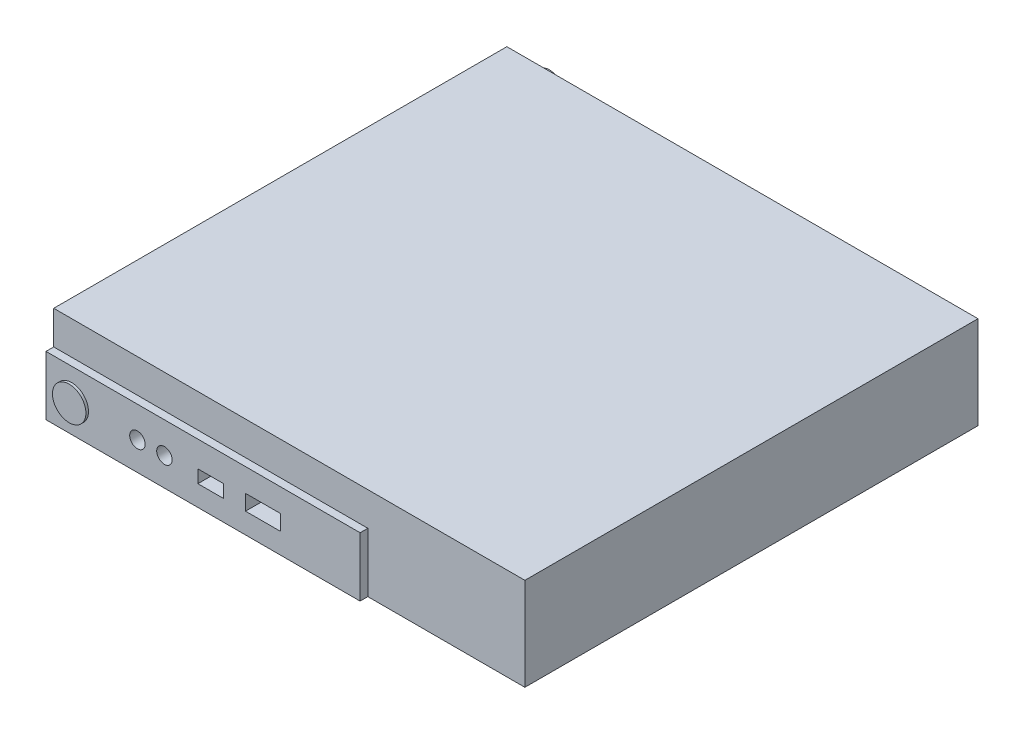
SolidWorks part; units mm, degrees
ref_plane "Front" through (0, 0, 0) normal (0, 0, 1) x (1, 0, 0)
ref_plane "Top" through (0, 0, 0) normal (0, 1, 0) x (1, 0, 0)
ref_plane "Right" through (0, 0, 0) normal (1, 0, 0) x (0, 0, -1)
sketch "草图1" plane through (0, 0, 0) normal (0, 1, 0) x (1, 0, 0)
  line L1 (-91.5, -89.5) -> (91.5, -89.5)
  line L2 (-91.5, -89.5) -> (-91.5, 89.5)
  line L3 (-91.5, 89.5) -> (91.5, 89.5)
  line L4 (91.5, -89.5) -> (91.5, 89.5)
  line L5 (-91.5, -89.5) -> (91.5, 89.5) construction
  line L6 (-91.5, 89.5) -> (91.5, -89.5) construction
  point P0 (0, 0)
  dimension "D1" = 179
  dimension "D2" = 183
extrude "凸台-拉伸1" add sketch "草图1" along normal blind 36
sketch "草图2" plane through (0, 0, 89.5) normal (0, 0, 1) x (1, 0, 0)
  line L0 (-91.5, 36) -> (-91.5, 23)
  line L1 (-91.5, 23) -> (30.5, 23)
  line L2 (30.5, 23) -> (30.5, 0)
  line L3 (-91.5, 0) -> (91.5, 0) construction
  line L4 (30.5, 0) -> (91.5, 0)
  line L5 (91.5, 0) -> (91.5, 36)
  line L6 (91.5, 36) -> (-91.5, 36)
  dimension "D1" = 122
  dimension "D2" = 23
extrude "切除-拉伸1" cut sketch "草图2" against normal blind 3
sketch "草图3" plane through (0, 0, 89.5) normal (0, 0, 1) x (1, 0, 0)
  line L0 (-91.5, 0) -> (30.5, 0) construction
  line L1 (-32.5, 13) -> (-22.5, 13)
  line L2 (-32.5, 13) -> (-32.5, 8)
  line L3 (-32.5, 8) -> (-22.5, 8)
  line L4 (-14, 14) -> (-0.5, 14)
  line L5 (-14, 14) -> (-14, 8)
  line L6 (-14, 8) -> (-0.5, 8)
  line L7 (-0.5, 14) -> (-0.5, 8)
  line L8 (-22.5, 13) -> (-22.5, 8)
  line L9 (30.5, 23) -> (30.5, 0) construction
  circle A0 centre (-56, 11) radius 3
  circle A1 centre (-45.5, 11) radius 3
  dimension "D1" = 6
  dimension "D2" = 6
  dimension "D11" = 10.5
  dimension "D12" = 11
  dimension "D3" = 10
  dimension "D4" = 5
  dimension "D5" = 13.5
  dimension "D6" = 6
  dimension "D7" = 8
  dimension "D8" = 31
  dimension "D9" = 8.5
  dimension "D10" = 13
extrude "切除-拉伸2" cut sketch "草图3" against normal blind 10
sketch "草图4" plane through (0, 0, 89.5) normal (0, 0, 1) x (1, 0, 0)
  line L0 (-91.5, 23) -> (-91.5, 0) construction
  line L1 (-91.5, 0) -> (30.5, 0) construction
  circle A0 centre (-81.5, 11) radius 6.5
  dimension "D1" = 13
  dimension "D3" = 11
  dimension "D2" = 10
extrude "凸台-拉伸2" add sketch "草图4" along normal blind 1
sketch "草图5" plane through (0, 0, -89.5) normal (0, 0, -1) x (-1, 0, 0)
  line L0 (-91.5, 36) -> (-91.5, 0) construction
  line L1 (-68.5, 14) -> (-51.5, 14)
  line L2 (-68.5, 14) -> (-68.5, 8)
  line L3 (-68.5, 8) -> (-51.5, 8)
  line L4 (-51.5, 14) -> (-51.5, 8)
  line L5 (-45.5, 14) -> (-28.5, 14)
  line L6 (-45.5, 14) -> (-45.5, 8)
  line L7 (-45.5, 8) -> (-28.5, 8)
  line L8 (-28.5, 14) -> (-28.5, 8)
  line L9 (-91.5, 0) -> (91.5, 0) construction
  line L10 (91.5, 36) -> (91.5, 0) construction
  line L11 (9.5, 22.5) -> (22.5, 22.5)
  line L12 (9.5, 22.5) -> (9.5, 16.5)
  line L13 (9.5, 16.5) -> (22.5, 16.5)
  line L14 (22.5, 22.5) -> (22.5, 16.5)
  line L15 (28.5, 22.5) -> (41.5, 22.5)
  line L16 (28.5, 22.5) -> (28.5, 16.5)
  line L17 (28.5, 16.5) -> (41.5, 16.5)
  line L18 (41.5, 22.5) -> (41.5, 16.5)
  line L19 (9.5, 14) -> (22.5, 14)
  line L20 (9.5, 14) -> (9.5, 8)
  line L21 (9.5, 8) -> (22.5, 8)
  line L22 (22.5, 14) -> (22.5, 8)
  line L23 (28.5, 14) -> (41.5, 14)
  line L24 (28.5, 14) -> (28.5, 8)
  line L25 (28.5, 8) -> (41.5, 8)
  line L26 (41.5, 14) -> (41.5, 8)
  line L28 (51.5, 15) -> (66.5, 15)
  line L29 (51.5, 15) -> (51.5, 4)
  line L30 (51.5, 4) -> (66.5, 4)
  line L31 (66.5, 15) -> (66.5, 4)
  circle A0 centre (-78, 11) radius 2.5
  dimension "D8" = 5
  dimension "D9" = 9.5
  dimension "D10" = 11
  dimension "D1" = 17
  dimension "D2" = 6
  dimension "D3" = 17
  dimension "D4" = 6
  dimension "D5" = 23
  dimension "D6" = 6
  dimension "D7" = 8
  dimension "D11" = 13
  dimension "D12" = 6
  dimension "D13" = 6
  dimension "D14" = 2.5
  dimension "D15" = 13
  dimension "D16" = 6
  dimension "D17" = 8
  dimension "D18" = 50
  dimension "D19" = 15
  dimension "D20" = 11
  dimension "D21" = 4
  dimension "D22" = 25
extrude "切除-拉伸3" cut sketch "草图5" against normal blind 10
sketch "草图6" plane through (0, 0, -89.5) normal (0, 0, -1) x (-1, 0, 0)
  line L0 (91.5, 36) -> (91.5, 0) construction
  line L1 (-91.5, 36) -> (91.5, 36) construction
  circle A0 centre (82.5, 24) radius 5
  dimension "D1" = 10
  dimension "D2" = 9
  dimension "D3" = 12
extrude "凸台-拉伸3" add sketch "草图6" along normal blind 7.5
